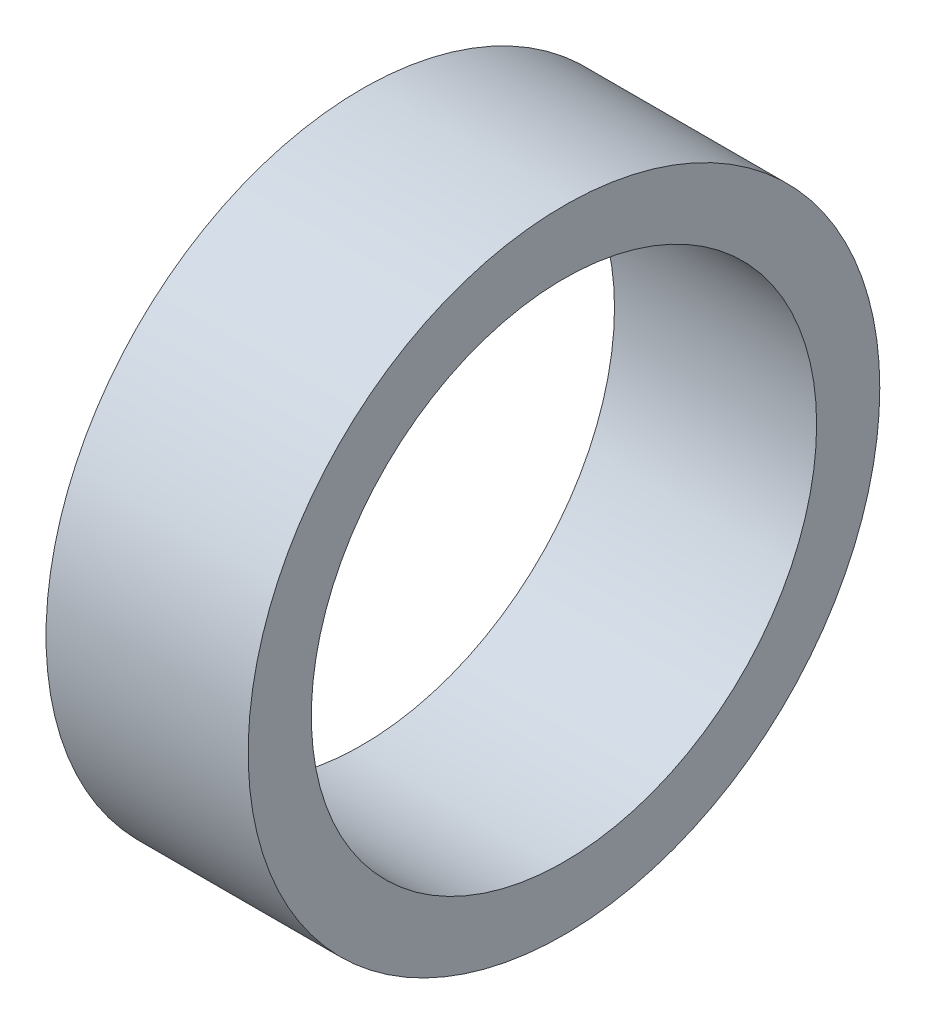
SolidWorks part; units mm, degrees
ref_plane "Front Plane" through (0, 0, 0) normal (0, 0, 1) x (1, 0, 0)
ref_plane "Top Plane" through (0, 0, 0) normal (0, 1, 0) x (1, 0, 0)
ref_plane "Right Plane" through (0, 0, 0) normal (1, 0, 0) x (0, 0, -1)
sketch "Sketch1" plane through (0, 0, 0) normal (1, 0, 0) x (0, 0, -1)
  circle A0 centre (0, 0) radius 12.5
  circle A1 centre (0, 0) radius 10
  dimension "D1" = 25
  dimension "D2" = 20
extrude "Boss-Extrude1" add sketch "Sketch1" along normal blind 8
